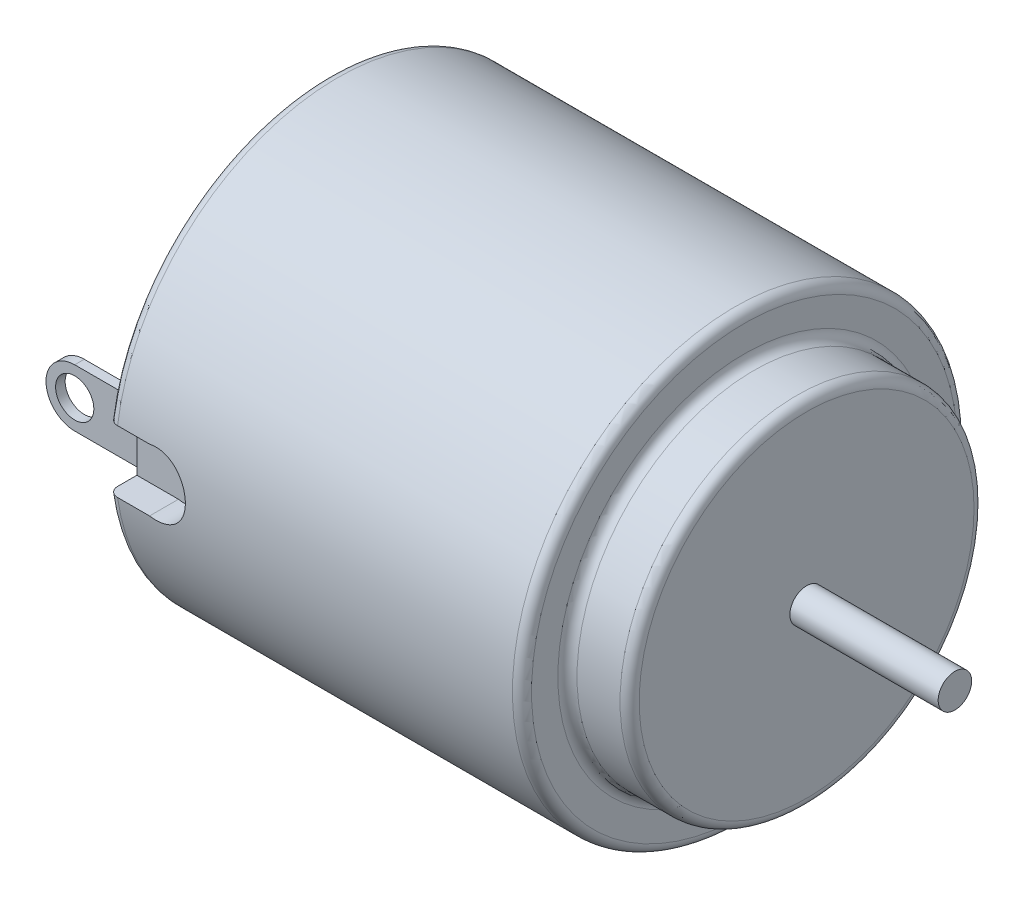
SolidWorks part; units mm, degrees
material "Chrome Stainless Steel"
ref_plane "Front Plane" through (0, 0, 0) normal (0, 0, 1) x (1, 0, 0)
ref_plane "Top Plane" through (0, 0, 0) normal (0, 1, 0) x (1, 0, 0)
ref_plane "Right Plane" through (0, 0, 0) normal (1, 0, 0) x (0, 0, -1)
sketch "Sketch2" plane through (0, 0, 0) normal (1, 0, 0) x (0, 0, -1)
  circle A0 centre (0, 0) radius 11.811
  dimension "D1" = 23.622
extrude "Boss-Extrude1" add sketch "Sketch2" along normal blind 25.4
sketch "Sketch4" plane through (25.4, 0, 0) normal (1, 0, 0) x (0, 0, -1)
  circle A0 centre (0, 0) radius 9.398
  dimension "D1" = 18.796
extrude "Cut-Extrude1" cut sketch "Sketch4" against normal blind 3.302 flip side to cut
fillet "Fillet1" radius 0.508 4 edges at (22.098, 0, -11.811) (0, 0, -11.811) (25.4, 0, -9.398) (22.098, 0, -9.398)
sketch "Sketch5" plane through (25.4, 0, 0) normal (1, 0, 0) x (0, 0, -1)
  circle A0 centre (0, 0) radius 0.889
  dimension "D1" = 1.778
extrude "Boss-Extrude2" add sketch "Sketch5" along normal blind 7.874
sketch "Sketch8" plane through (0, 0, 0) normal (0, 0, 1) x (1, 0, 0)
  line L1 (0, -1.651) -> (2.54, -1.651)
  line L2 (0, -1.651) -> (0, 1.651)
  line L3 (0, 1.651) -> (2.54, 1.651)
  line L4 (2.54, -1.651) -> (2.54, 1.651)
  circle A0 centre (2.54, 0) radius 1.6842
  dimension "D1" = 2.54
  dimension "D2" = 3.302
extrude "Cut-Extrude2" cut sketch "Sketch8" along normal through all from offset 10.16 contours L2 L3 L4 L1 | A0
sketch "Sketch10" plane through (0, 0, 0) normal (0, 0, 1) x (1, 0, 0)
  line L1 (-3.556, -1.524) -> (0, -1.524)
  line L2 (-3.556, -1.524) -> (-3.556, 1.524)
  line L3 (-3.556, 1.524) -> (0, 1.524)
  line L4 (0, -1.524) -> (0, 1.524)
  circle A0 centre (-3.556, 0) radius 1.524
  circle A1 centre (-3.556, 0) radius 1.016
  dimension "D1" = 3.048
  dimension "D3" = 2.032
  dimension "D2" = 3.556
extrude "Boss-Extrude3" add sketch "Sketch10" along normal blind 0.508 from offset 9.398 contours A0 L1 L4 L3 | A1
pattern_circular "CirPattern1" count 2 over 360 about axis through (0, 0, 0) along (1, 0, 0) of "Boss-Extrude3"
